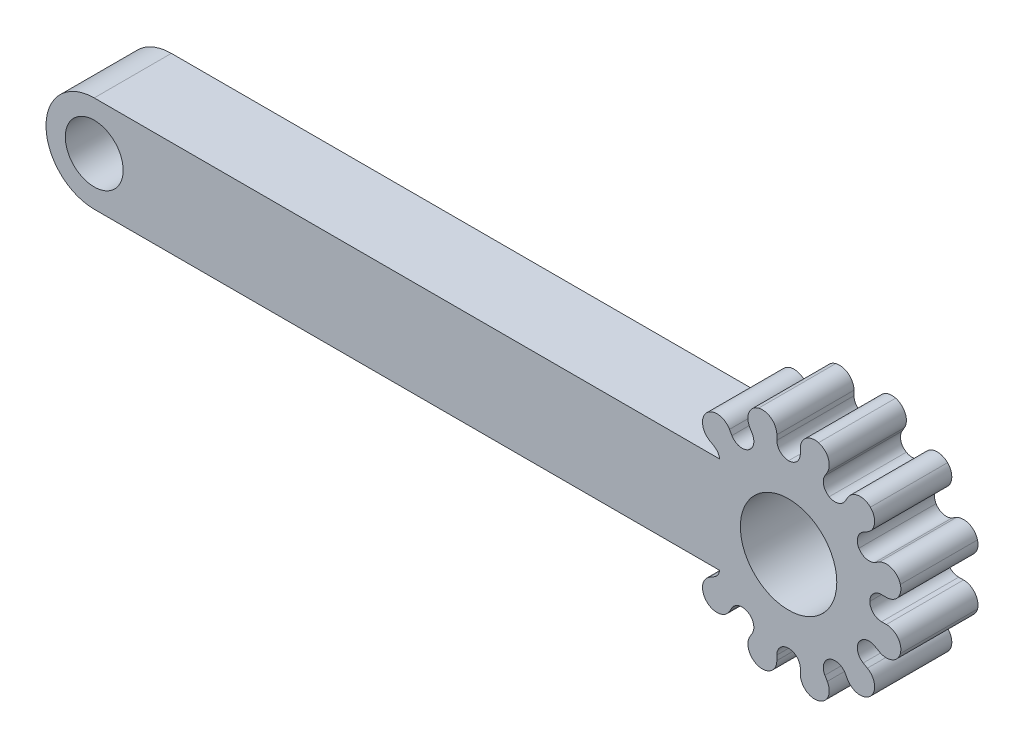
SolidWorks part; units mm, degrees
ref_plane "Front Plane" through (0, 0, 0) normal (0, 0, 1) x (1, 0, 0)
ref_plane "Top Plane" through (0, 0, 0) normal (0, 1, 0) x (1, 0, 0)
ref_plane "Right Plane" through (0, 0, 0) normal (1, 0, 0) x (0, 0, -1)
sketch "Sketch1" plane through (0, 0, 0) normal (0, 0, 1) x (1, 0, 0)
  line L0 (-18, 0) -> (18, 0) construction
  line L1 (-18, 0) -> (-18, -2.5) construction
  line L2 (-18, 0) -> (-18, 2.5) construction
  line L3 (-18, 2.5) -> (12.5456, 2.5)
  line L4 (-18, -2.5) -> (12.5456, -2.5)
  circle A0 centre (-18, 0) radius 1.5
  arc A1 (-18, 2.5) -> (-18, -2.5) centre (-18, 0) ccw
  arc A2 (12.5456, -2.5) -> (12.5456, 2.5) centre (18, 0) ccw
  point P4 (0, 0)
  dimension "D2" = 3
  dimension "D3" = 5
  dimension "D4" = 12
  dimension "D1" = 36
extrude "Boss-Extrude1" add sketch "Sketch1" along normal blind 4
sketch "Sketch2" plane through (0, 0, 4) normal (0, 0, 1) x (1, 0, 0)
  line L0 (18, 6) -> (18, -6) construction
  line L1 (18, 0) -> (22.2426, 4.2426) construction
  line L2 (18, 0) -> (19.5529, 5.7956) construction
  line L4 (18, 0) -> (20.105, 3.646) construction
  line L6 (20.0081, 4.6956) -> (19.8829, 4.4792)
  line L7 (21.0624, 4.0868) -> (20.9376, 3.8702)
  arc A0 (19.5529, 5.7956) -> (20.0081, 4.6956) centre (19.3589, 5.0711) cw
  arc A6 (12.5456, -2.5) -> (12.5456, 2.5) centre (18, 0) ccw construction
  arc A7 (19.8829, 4.4792) -> (20.105, 3.646) centre (20.4109, 4.1737) ccw
  arc A8 (20.9376, 3.8702) -> (20.105, 3.646) centre (20.4091, 4.1748) cw
  arc A9 (22.2426, 4.2426) -> (21.0624, 4.0868) centre (21.7123, 3.7124) ccw
  arc A10 (19.5529, 5.7956) -> (22.2426, 4.2426) centre (19.9681, 3.4089) cw
  dimension "D6" = 1.1
  dimension "D7" = 0.25
  dimension "D5" = 0.75
  dimension "D8" = 0.61
  dimension "D1" = 15
  dimension "D2" = 30
  dimension "D3" = 4.21
  dimension "D4" = 15
extrude "Cut-Extrude2" cut sketch "Sketch2" against normal through all
pattern_circular "CirPattern1" count 12 over 360 about axis through (18, 0, 0) along (0, 0, 1) of "Cut-Extrude2"
sketch "Sketch3" plane through (0, 0, 4) normal (0, 0, 1) x (1, 0, 0)
  line L0 (12.2277, 2.5) -> (-18, 2.5) construction
  line L1 (8.0978, 2.5) -> (15.9609, 2.5)
  line L2 (8.0978, 2.5) -> (8.0978, -2.5)
  line L3 (8.0978, -2.5) -> (15.9609, -2.5)
  line L4 (15.9609, 2.5) -> (15.9609, -2.5)
  line L5 (-18, -2.5) -> (12.2277, -2.5) construction
extrude "Boss-Extrude2" add sketch "Sketch3" against normal blind 4
sketch "Sketch4" plane through (0, 0, 4) normal (0, 0, 1) x (1, 0, 0)
  line L0 (18, 6) -> (18, -6) construction
  circle A0 centre (18, 0) radius 2.5
  dimension "D1" = 5
extrude "Cut-Extrude3" cut sketch "Sketch4" against normal through all
